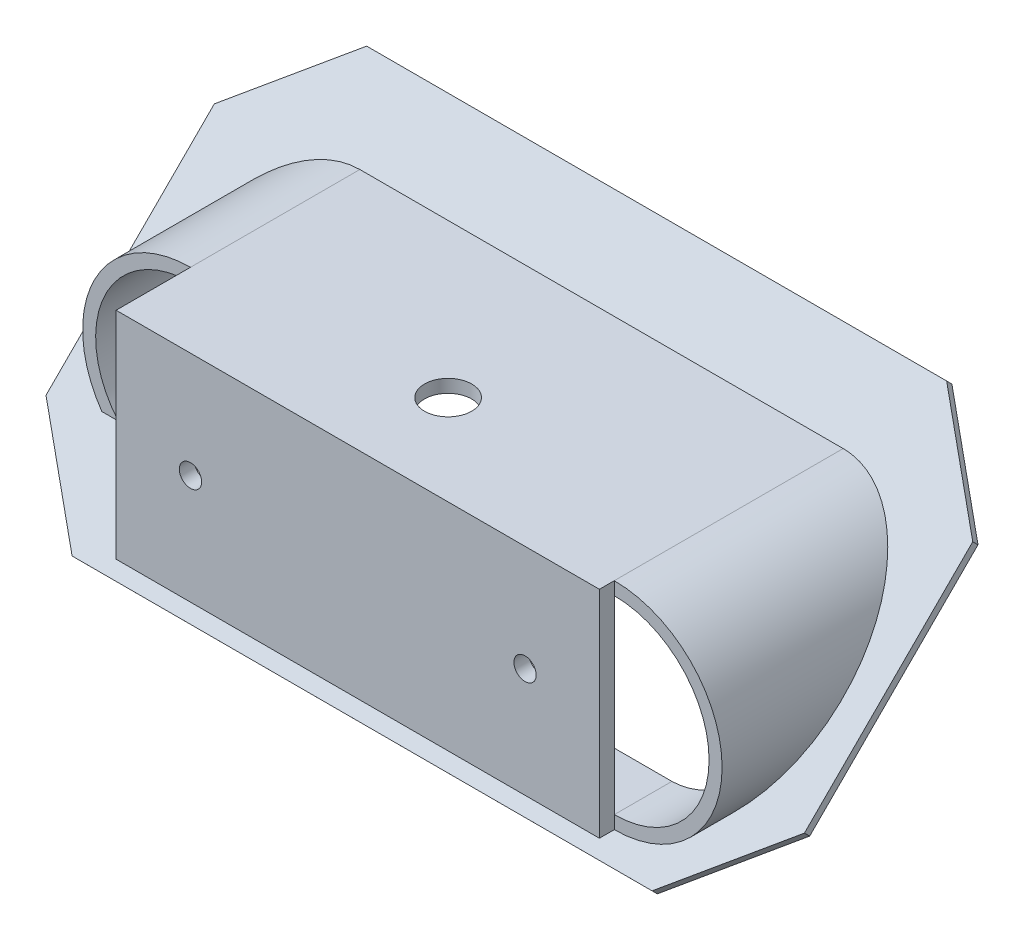
SolidWorks part; units mm, degrees
ref_plane "Front Plane" through (0, 0, 0) normal (0, 0, 1) x (1, 0, 0)
ref_plane "Top Plane" through (0, 0, 0) normal (0, 1, 0) x (1, 0, 0)
ref_plane "Right Plane" through (0, 0, 0) normal (1, 0, 0) x (0, 0, -1)
sketch "Sketch22" plane through (0, 0, 0) normal (0, 0, 1) x (1, 0, 0)
  line L3 (32.5, 0) -> (-32.5, 0) construction
  line L10 (32.5, -14.5) -> (-32.5, -14.5)
  line L11 (32.5, 14.5) -> (-32.5, 14.5)
  arc A2 (32.5, -14.5) -> (32.5, 14.5) centre (32.5, 0) ccw
  arc A3 (-32.5, 14.5) -> (-32.5, -14.5) centre (-32.5, 0) ccw
  point P8 (0, 0)
  point P15 (0, 0)
extrude "Boss-Extrude12" add sketch "Sketch22" along normal blind 80
sketch "Sketch34" plane through (0, 0, 0) normal (0, 0, -1) x (-1, 0, 0)
  line L0 (32.5, -14.5) -> (32.5, 14.5) construction
ref_plane "Plane5" through (-32.5, 0, 0) normal (1, 0, 0) x (0, 0, -1)
sketch "Sketch35" plane through (-32.5, 0, 0) normal (1, 0, 0) x (0, 0, -1)
  line L0 (0, 14.5) -> (-29.0269, -14.5)
  line L1 (-80, -14.5) -> (0, -14.5) construction
  line L2 (-29.0269, -14.5) -> (0, -14.5)
  line L3 (0, -14.5) -> (0, 14.5)
extrude "Cut-Extrude10" cut sketch "Sketch35" against normal through all and the other way through all
ref_plane "Plane6" through (0, 7.2567, 7.25) normal (0, -0.7074, -0.7068) x (-1, 0, 0)
sketch "Sketch37" plane through (0, 7.2567, 7.25) normal (0, -0.7074, -0.7068) x (-1, 0, 0)
  line L0 (0, 10.2483) -> (0, -30.7829) construction
  line L1 (-32.5, 10.2483) -> (32.5, 10.2483) construction
  line L2 (32.5, -30.7829) -> (-32.5, -30.7829) construction
  line L4 (51, 17.7327) -> (-51, 17.7327)
  line L5 (51, 17.7327) -> (51, -38.2673)
  line L6 (51, -38.2673) -> (-51, -38.2673)
  line L7 (-51, 17.7327) -> (-51, -38.2673)
  line L8 (51, 17.7327) -> (-51, -38.2673) construction
  line L9 (51, -38.2673) -> (-51, 17.7327) construction
  point P6 (0, -10.2673)
extrude "Boss-Extrude16" add sketch "Sketch37" against normal blind 3
sketch "Sketch38" plane through (0, 0, 80) normal (0, 0, 1) x (1, 0, 0)
  line L0 (32.5, -14.5) -> (32.5, 14.5)
  line L1 (-32.5, 0) -> (32.5, 0) construction
  line L2 (-32.5, 12.75) -> (32.5, 12.75)
  line L3 (-32.5, -12.75) -> (32.5, -12.75)
  arc A0 (-32.5, 12.75) -> (-32.5, -12.75) centre (-32.5, 0) ccw
  arc A1 (32.5, -12.75) -> (32.5, 12.75) centre (32.5, 0) ccw
  point P6 (0, 0)
extrude "Cut-Extrude11" cut sketch "Sketch38" against normal through all contours L3 A1 L2 A0
sketch "Sketch40" plane through (0, -12.75, 0) normal (0, 1, 0) x (1, 0, 0)
  line L0 (32.5, -27.2752) -> (32.5, -35.025) construction
  line L1 (32.5, -27.2752) -> (32.5, -80) construction
  line L2 (-32.5, -27.2752) -> (-32.5, -35.025) construction
  line L3 (-32.5, -27.2752) -> (-32.5, -80) construction
  line L4 (-32.5, -35.025) -> (32.5, -35.025) construction
  line L6 (69.7281, -35.025) -> (-57.7587, -35.025)
  line L7 (-57.7587, -35.025) -> (-57.7587, -89.8582)
  line L8 (-57.7587, -89.8582) -> (69.7281, -89.8582)
  line L9 (69.7281, -89.8582) -> (69.7281, -35.025)
extrude "Cut-Extrude12" cut sketch "Sketch40" along normal through all and the other way up to surface (1.75 mm away) other way up to face at (0, -14.5, 56.6357)
sketch "Sketch42" plane through (-51, 0, 0) normal (-1, 0, 0) x (0, 0, 1)
  line L0 (35.025, 14.5) -> (27.025, 14.5)
  line L1 (35.025, 14.5) -> (4.2446, 14.5) construction
  line L2 (27.025, 14.5) -> (27.025, -8.2593)
  line L3 (36.4419, -17.6675) -> (-3.1744, 21.9121) construction
  line L4 (27.025, -8.2593) -> (33.2715, -14.5)
  line L5 (33.2715, -14.5) -> (35.025, -14.5)
  line L6 (35.025, -14.5) -> (35.025, 14.5)
extrude "Cut-Extrude14" cut sketch "Sketch42" against normal up to vertex (18.5 mm away) up to point (-32.5, -12.75, 35.025)
hole_wizard "1/4 (0.25) Diameter Hole1" positions "Sketch46" profile "Sketch48" hole size "1/4" standard "ANSI Inch"
sketch "Sketch46" plane through (0, 14.5, 0) normal (0, 1, 0) x (1, 0, 0)
  point P2 (0, -24.875)
sketch "Sketch48" plane through (0, 14.5, 24.875) normal (1, 0, 0) x (0, 0, 1)
  line L0 (0, 0) -> (0, 6.9077)
  line L1 (0, 6.9077) -> (3.175, 5)
  line L2 (3.175, 5) -> (3.175, 0)
  line L5 (3.175, 0) -> (0, 0)
  line L10 (0, 6.9077) -> (-3.175, 5) construction
  line L11 (0, -6.35) -> (0, 107.95) construction
  dimension "Hole Dia." = 6.35
  dimension "Hole Depth" = 5
  dimension "Drill Angle" = 118
chamfer "Chamfer2" distance 12 angle 45 4 edges at (-51, 20.851, -4.2346) (51, 20.851, -4.2346) (51, -18.7287, 35.3818) (-51, -18.7287, 35.3818)
chamfer "Chamfer3" distance 2 angle 45 8 edges at (45, -15.5491, 30.077) (51, 0, 14.5134) (45, 15.5491, -1.0501) (0, 19.7898, -5.2947) (0, -19.7898, 34.3216) (-45, -15.5491, 30.077) (-51, 0, 14.5134) (-45, 15.5491, -1.0501)
sketch "Sketch49" plane through (0, 12.75, 0) normal (0, -1, 0) x (-1, 0, 0)
  line L0 (0, -1.7516) -> (0, -35.025)
  line L1 (32.5, -1.7516) -> (-32.5, -1.7516) construction
  line L2 (-32.5, -35.025) -> (32.5, -35.025) construction
sketch "Sketch50" plane through (0, 14.5, 0) normal (0, 1, 0) x (1, 0, 0)
  line L0 (32.5, -35.025) -> (32.5, -37.025)
  line L1 (-32.5, -35.025) -> (-32.5, -37.025)
  line L2 (-32.5, -37.025) -> (32.5, -37.025)
  line L3 (32.5, -35.025) -> (-32.5, -35.025)
extrude "Boss-Extrude17" add sketch "Sketch50" against normal up to vertex (31.5839 mm away)
hole_wizard "Ø3.0mm Dowel Hole1" positions "Sketch53" profile "Sketch52" hole size "Ø3.0" standard "ANSI Metric" end condition up to next
sketch "Sketch53" plane through (0, 0, 35.025) normal (0, 0, -1) x (-1, 0, 0)
  point P0 (-22.5, 0.25)
  point P3 (22.5, 0.25)
sketch "Sketch52" plane through (22.5, 0.25, 35.025) normal (1, 0, 0) x (0, 1, 0)
  line L0 (0, 0) -> (0, 2)
  line L1 (0, 2) -> (1.5, 2)
  line L2 (1.5, 2) -> (1.5, 0)
  line L5 (1.5, 0) -> (0, 0)
  line L11 (0, -6.35) -> (0, 107.95) construction
  dimension "Thru Hole Dia." = 3
  dimension "Thru Hole Depth" = 2
